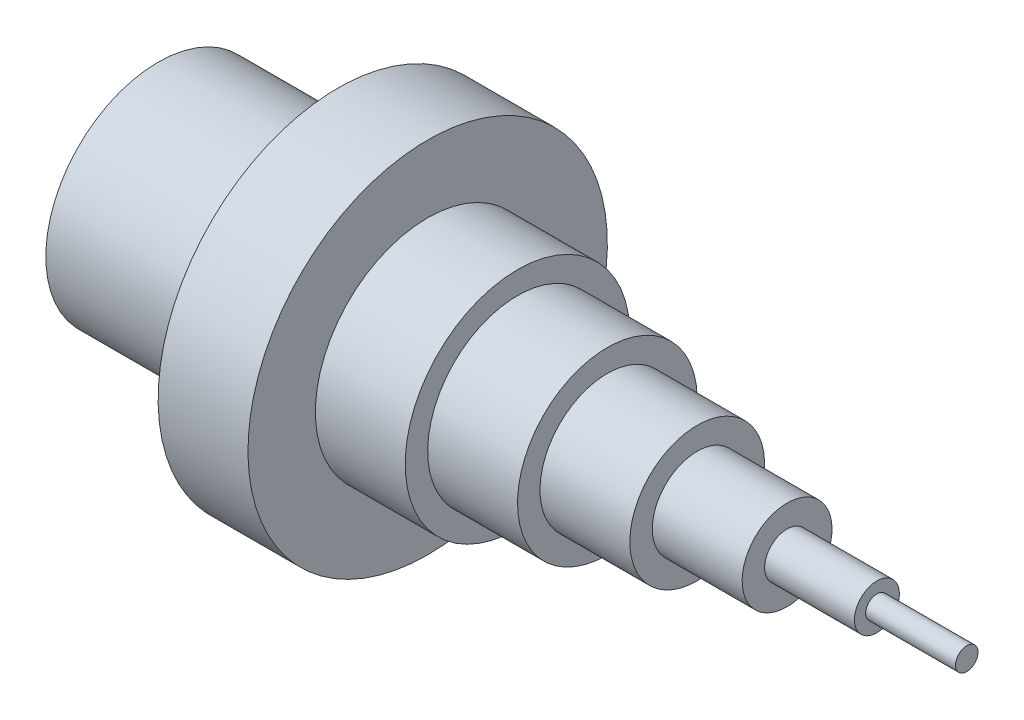
SolidWorks part; units mm, degrees
ref_plane "Front Plane" through (0, 0, 0) normal (0, 0, 1) x (1, 0, 0)
ref_plane "Top Plane" through (0, 0, 0) normal (0, 1, 0) x (1, 0, 0)
ref_plane "Right Plane" through (0, 0, 0) normal (1, 0, 0) x (0, 0, -1)
sketch "Sketch1" plane through (0, 0, 0) normal (0, 0, 1) x (1, 0, 0)
  line L0 (-74.7901, 0) -> (139.7743, 0) construction
  line L1 (-40.2257, 20) -> (-40.2257, 25)
  line L2 (-40.2257, 25) -> (-0.2257, 25)
  line L3 (-0.2257, 25) -> (-0.2257, 40)
  line L4 (-0.2257, 40) -> (19.7743, 40)
  line L5 (19.7743, 40) -> (19.7743, 25)
  line L6 (19.7743, 25) -> (39.7743, 25)
  line L7 (39.7743, 25) -> (39.7743, 20)
  line L8 (39.7743, 20) -> (59.7743, 20)
  line L9 (59.7743, 20) -> (59.7743, 15)
  line L10 (59.7743, 15) -> (79.7743, 15)
  line L11 (79.7743, 15) -> (79.7743, 10)
  line L12 (79.7743, 10) -> (99.7743, 10)
  line L13 (99.7743, 10) -> (99.7743, 5)
  line L14 (99.7743, 5) -> (119.7743, 5)
  line L15 (119.7743, 5) -> (119.7743, 2.5)
  line L16 (119.7743, 2.5) -> (139.7743, 2.5)
  line L17 (139.7743, 2.5) -> (139.7743, 0)
  line L18 (139.7743, 0) -> (-0.123, 0)
  line L19 (-40.2257, 20) -> (-0.123, 20)
  line L20 (-0.123, 20) -> (-0.123, 0)
  dimension "D1" = 40
  dimension "D2" = 20
  dimension "D3" = 20
  dimension "D4" = 20
  dimension "D5" = 20
  dimension "D6" = 20
  dimension "D7" = 50
  dimension "D8" = 50
  dimension "D9" = 80
  dimension "D10" = 40
  dimension "D11" = 30
  dimension "D12" = 20
  dimension "D13" = 10
  dimension "D14" = 5
revolve "Revolve2" add sketch "Sketch1" angle 360 about L0
